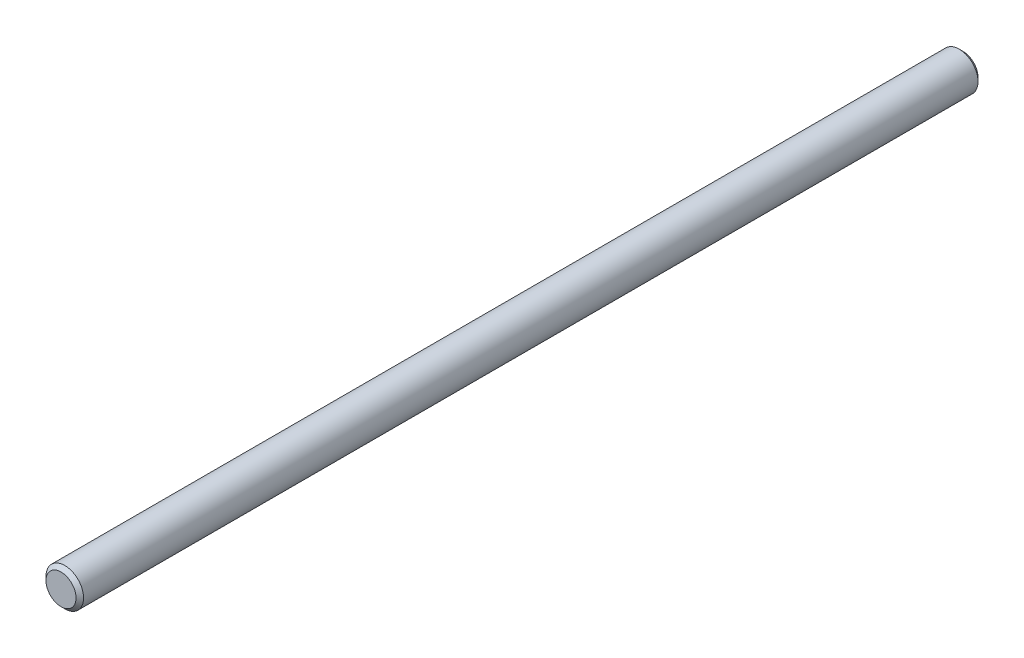
SolidWorks part; units mm, degrees
ref_plane "Front" through (0, 0, 0) normal (0, 0, 1) x (1, 0, 0)
ref_plane "Top" through (0, 0, 0) normal (0, 1, 0) x (1, 0, 0)
ref_plane "Right" through (0, 0, 0) normal (1, 0, 0) x (0, 0, -1)
sketch "Sketch1" plane through (0, 0, 0) normal (0, 0, 1) x (1, 0, 0)
  circle A0 centre (0, 0) radius 3.175
  dimension "dia" = 6.35
extrude "Extrude1" add sketch "Sketch1" along normal mid plane 152.4
sketch "Sketch2" plane through (0, 0, 0) normal (1, 0, 0) x (0, 0, -1)
  point P0 (-76.2, 3.175)
  point P1 (76.2, 3.175)
chamfer "Chamfer1" distance 0.635 angle 45 2 edges at (3.175, 0, -76.2) (3.175, 0, 76.2)
equation "\"D1@Chamfer1\" = \"dia@Sketch1\" * .1"
